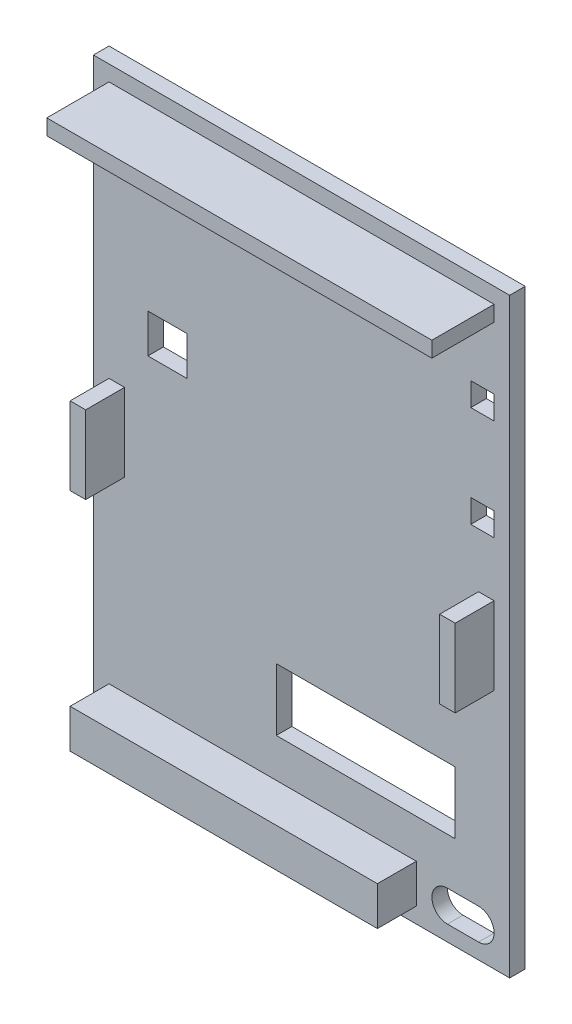
SolidWorks part; units mm, degrees
ref_plane "Front Plane" through (0, 0, 0) normal (0, 0, 1) x (1, 0, 0)
ref_plane "Top Plane" through (0, 0, 0) normal (0, 1, 0) x (1, 0, 0)
ref_plane "Right Plane" through (0, 0, 0) normal (1, 0, 0) x (0, 0, -1)
sketch "Sketch1" plane through (0, 0, 0) normal (0, 0, 1) x (1, 0, 0)
  line L1 (-54.4258, 31.9075) -> (-0.9258, 31.9075)
  line L2 (-54.4258, 31.9075) -> (-54.4258, -44.0925)
  line L3 (-54.4258, -44.0925) -> (-0.9258, -44.0925)
  line L4 (-0.9258, 31.9075) -> (-0.9258, -44.0925)
  dimension "D1" = 76
  dimension "D2" = 53.5
extrude "Boss-Extrude1" add sketch "Sketch1" along normal blind 2
sketch "Sketch5" plane through (0, 0, 2) normal (0, 0, 1) x (1, 0, 0)
  line L2 (-52.4258, 29.9075) -> (-52.4258, 27.9075)
  line L6 (-54.4258, 31.9075) -> (-54.4258, -44.0925) construction
  line L7 (-0.9258, -44.0925) -> (-0.9258, 31.9075) construction
  line L12 (-2.9258, 29.9075) -> (-52.4258, 29.9075)
  line L13 (-2.9258, 29.9075) -> (-2.9258, 27.9075)
  line L16 (-0.9258, 31.9075) -> (-54.4258, 31.9075) construction
  line L19 (-2.9258, 27.9075) -> (-52.4258, 27.9075)
  dimension "D1" = 2
  dimension "D2" = 2
  dimension "D4" = 2
  dimension "D7" = 2
extrude "Boss-Extrude2" add sketch "Sketch5" along normal blind 8 contours L19 L13 L12 L2
sketch "Sketch6" plane through (0, 0, 2) normal (0, 0, 1) x (1, 0, 0)
  line L1 (-2.9258, -3.0925) -> (-4.9258, -3.0925)
  line L2 (-2.9258, -3.0925) -> (-2.9258, -13.0925)
  line L3 (-2.9258, -13.0925) -> (-4.9258, -13.0925)
  line L4 (-4.9258, -3.0925) -> (-4.9258, -13.0925)
  line L7 (-0.9258, -44.0925) -> (-0.9258, 31.9075) construction
  line L8 (-0.9258, 31.9075) -> (-54.4258, 31.9075) construction
  line L9 (-27.6758, 27.9075) -> (-27.6758, -44.0925) construction
  line L10 (-2.9258, 27.9075) -> (-52.4258, 27.9075) construction
  line L11 (-54.4258, -44.0925) -> (-0.9258, -44.0925) construction
  line L12 (-52.4258, -13.0925) -> (-50.4258, -13.0925)
  line L13 (-50.4258, -3.0925) -> (-50.4258, -13.0925)
  line L14 (-52.4258, -3.0925) -> (-50.4258, -3.0925)
  line L15 (-52.4258, -3.0925) -> (-52.4258, -13.0925)
  dimension "D1" = 2
  dimension "D2" = 2
  dimension "D3" = 10
  dimension "D4" = 35
extrude "Boss-Extrude3" add sketch "Sketch6" along normal blind 5
sketch "Sketch7" plane through (0, 0, 2) normal (0, 0, 1) x (1, 0, 0)
  line L0 (-54.4258, -44.0925) -> (-0.9258, -44.0925) construction
  line L1 (-52.4258, -37.0925) -> (-12.9258, -37.0925)
  line L2 (-52.4258, -37.0925) -> (-52.4258, -42.0925)
  line L3 (-52.4258, -42.0925) -> (-12.9258, -42.0925)
  line L4 (-12.9258, -37.0925) -> (-12.9258, -42.0925)
  line L5 (-54.4258, 31.9075) -> (-54.4258, -44.0925) construction
  line L6 (-0.9258, -44.0925) -> (-0.9258, 31.9075) construction
  dimension "D1" = 5
  dimension "D2" = 2
  dimension "D3" = 2
  dimension "D4" = 12
extrude "Boss-Extrude4" add sketch "Sketch7" along normal blind 5
sketch "Sketch9" plane through (0, 0, 0) normal (0, 0, -1) x (-1, 0, 0)
  text T0 "<b><r180>P   OI</r></b>" font "Century Gothic" height in points 36
extrude "Cut-Extrude1" cut sketch "Sketch9" against normal blind 1.5
sketch "Sketch10" plane through (0, 0, 0) normal (0, 0, -1) x (-1, 0, 0)
  line L0 (54.4258, -44.0925) -> (0.9258, -44.0925) construction
  line L1 (7.9258, -24.0925) -> (30.9258, -24.0925)
  line L2 (7.9258, -24.0925) -> (7.9258, -32.0925)
  line L3 (7.9258, -32.0925) -> (30.9258, -32.0925)
  line L4 (30.9258, -24.0925) -> (30.9258, -32.0925)
  line L5 (0.9258, -44.0925) -> (0.9258, 31.9075) construction
  line L10 (54.4258, 31.9075) -> (54.4258, -44.0925) construction
  line L11 (42.4258, 6.9075) -> (47.4258, 6.9075)
  line L12 (42.4258, 6.9075) -> (42.4258, 1.9075)
  line L13 (42.4258, 1.9075) -> (47.4258, 1.9075)
  line L14 (47.4258, 6.9075) -> (47.4258, 1.9075)
  line L15 (0.9258, 31.9075) -> (54.4258, 31.9075) construction
  line L16 (2.9258, 6.9075) -> (5.9258, 6.9075)
  line L17 (2.9258, 19.9075) -> (5.9258, 19.9075)
  line L18 (2.9258, 19.9075) -> (2.9258, 16.9075)
  line L19 (2.9258, 16.9075) -> (5.9258, 16.9075)
  line L20 (5.9258, 19.9075) -> (5.9258, 16.9075)
  line L21 (2.9258, 6.9075) -> (2.9258, 3.9075)
  line L22 (2.9258, 3.9075) -> (5.9258, 3.9075)
  line L23 (5.9258, 6.9075) -> (5.9258, 3.9075)
  dimension "D1" = 30
  dimension "D2" = 8
  dimension "D3" = 12
  dimension "D4" = 7
  dimension "D5" = 5
  dimension "D6" = 5
  dimension "D7" = 7
  dimension "D8" = 25
  dimension "D9" = 12
  dimension "D10" = 3
  dimension "D11" = 3
  dimension "D12" = 2
  dimension "D13" = 10
  dimension "D14" = 2
  dimension "D15" = 3
  dimension "D16" = 3
extrude "Cut-Extrude2" cut sketch "Sketch10" against normal blind 3 contours L18 L17 L20 L19 | L16 L23 L22 L21 | L12 L11 L14 L13 | L2 L1 L4 L3
sketch "Sketch11" plane through (0, 0, 2) normal (0, 0, 1) x (1, 0, 0)
  line L0 (-0.9258, -44.0925) -> (-0.9258, 31.9075) construction
  line L2 (-54.4258, -44.0925) -> (-0.9258, -44.0925) construction
  line L3 (-4.9258, -38.0925) -> (-8.9258, -38.0925)
  line L4 (-8.9258, -42.0925) -> (-4.9258, -42.0925)
  arc A0 (-4.9258, -42.0925) -> (-4.9258, -38.0925) centre (-4.9258, -40.0925) ccw
  arc A1 (-8.9258, -38.0925) -> (-8.9258, -42.0925) centre (-8.9258, -40.0925) ccw
  dimension "D1" = 4
  dimension "D2" = 4
  dimension "D3" = 4
  dimension "D4" = 4
extrude "Cut-Extrude3" cut sketch "Sketch11" against normal blind 10
